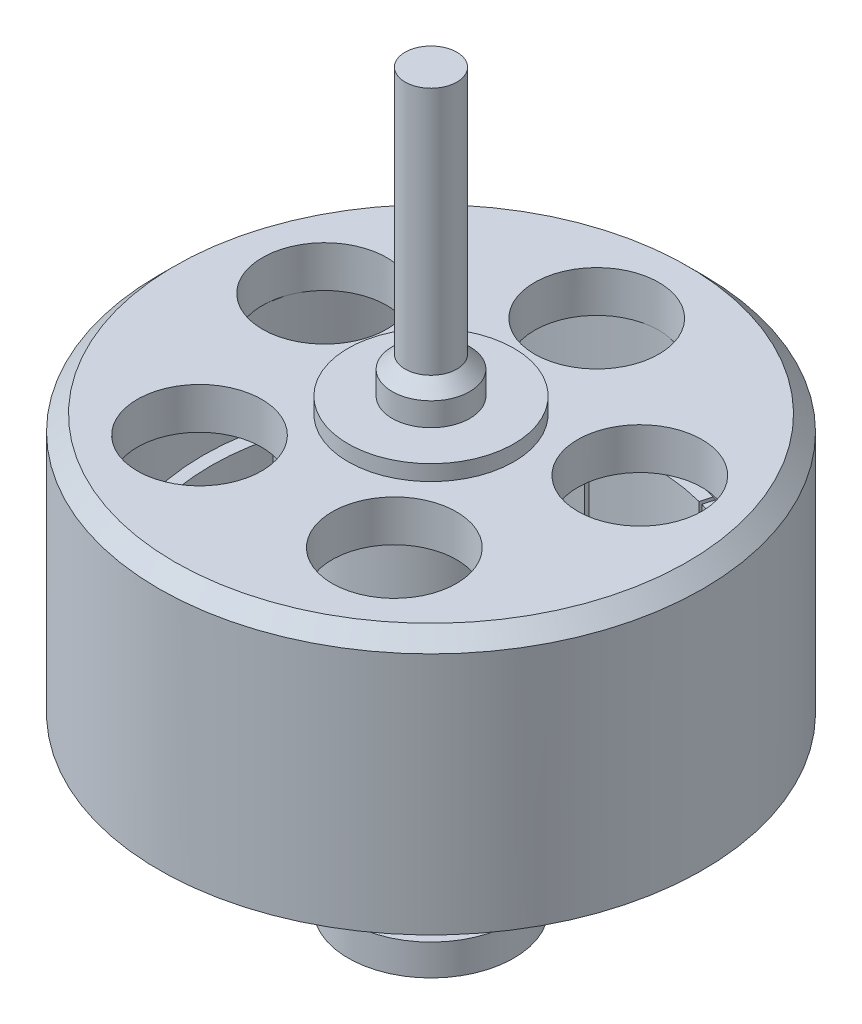
SolidWorks part; units mm, degrees
ref_plane "Front Plane" through (0, 0, 0) normal (0, 0, 1) x (1, 0, 0)
ref_plane "Top Plane" through (0, 0, 0) normal (0, 1, 0) x (1, 0, 0)
ref_plane "Right Plane" through (0, 0, 0) normal (1, 0, 0) x (0, 0, -1)
sketch "Sketch2" plane through (0, 0, 0) normal (1, 0, 0) x (0, 0, -1)
  line L0 (0, -2.1) -> (0, 2.1) construction
  line L1 (0, 2.1) -> (4.9, 2.1)
  line L2 (4.9, 2.1) -> (4.9, -2.1)
  line L3 (4.9, -2.1) -> (5.25, -2.1)
  line L4 (5.25, -2.1) -> (5.25, 2.9)
  line L5 (5.25, 2.9) -> (0, 2.9)
  line L6 (0, 2.9) -> (0, 2.1)
  point P4 (0, 0)
  dimension "D1" = 5.25
  dimension "D2" = 4.2
  dimension "D3" = 0.35
  dimension "D4" = 5
revolve "Revolve1" add sketch "Sketch2" angle 360 about L0
sketch "Sketch3" plane through (0, 2.9, 0) normal (0, 1, 0) x (1, 0, 0)
  line L1 (0, 3.2) -> (-3.0434, 0.9889) construction
  line L2 (-3.0434, 0.9889) -> (-1.8809, -2.5889) construction
  line L3 (-1.8809, -2.5889) -> (1.8809, -2.5889) construction
  line L4 (1.8809, -2.5889) -> (3.0434, 0.9889) construction
  line L5 (3.0434, 0.9889) -> (0, 3.2) construction
  circle A0 centre (0, 0) radius 2.5889 construction
  circle A1 centre (0, 3.2) radius 1.2
  circle A2 centre (3.0434, 0.9889) radius 1.2
  circle A3 centre (1.8809, -2.5889) radius 1.2
  circle A4 centre (-1.8809, -2.5889) radius 1.2
  circle A5 centre (-3.0434, 0.9889) radius 1.2
  circle A6 centre (0, 0) radius 5.25 construction
  point P13 (0, 4.4)
  point P16 (0, 5.25)
  dimension "D1" = 2.4
  dimension "D2" = 0.85
extrude "Cut-Extrude1" cut sketch "Sketch3" against normal through all
sketch "Sketch4" plane through (0, -2.1, 0) normal (0, -1, 0) x (1, 0, 0)
  line L0 (1.0641, -4.1146) -> (1.2269, -4.7439)
  line L1 (-1.0641, -4.1146) -> (-1.2269, -4.7439)
  line L2 (-1.0641, -4.1146) -> (0, 0) construction
  line L3 (0, 0) -> (1.0641, -4.1146) construction
  arc A0 (1.0641, -4.1146) -> (-1.0641, -4.1146) centre (0, 0) cw
  arc A1 (1.2269, -4.7439) -> (-1.2269, -4.7439) centre (0, 0) cw
  circle A2 centre (0, 0) radius 4.9 construction
  circle A3 centre (0, 0) radius 5.25 construction
  point P9 (0, -5.25)
  point P13 (0, -4.25)
  dimension "D1" = 29
  dimension "D2" = 1
extrude "Boss-Extrude1" add sketch "Sketch4" against normal blind 2 from offset 0.01 offset against normal yes
pattern_circular "CirPattern1" count 12 over 360 about axis through (0, 0, 0) along (0, 1, 0) of "Boss-Extrude1"
chamfer "Chamfer1" distance 0.3 angle 45 1 edges at (0, 2.9, -5.25)
sketch "Sketch6" plane through (0, 0, 0) normal (0, 0, 1) x (1, 0, 0)
  line L0 (4.95, 2.9) -> (-4.95, 2.9) construction
  line L1 (0, -6.1) -> (0.5, -6.1)
  line L2 (0, -6.1) -> (0, 8.7)
  line L3 (0, 8.7) -> (0.5, 8.7)
  line L4 (0.5, -6.1) -> (0.5, 8.7)
  line L5 (-5.25, -2.1) -> (5.25, -2.1) construction
  dimension "D1" = 5.8
  dimension "D2" = 0.5
  dimension "D3" = 4
revolve "Revolve2" add sketch "Sketch6" angle 360 about L2
sketch "Sketch7" plane through (0, 0, 0) normal (0, 0, 1) x (1, 0, 0)
  line L0 (-0.5, -6.1) -> (0.5, -6.1) construction
  line L1 (0, 2.9) -> (1.6, 2.9)
  line L2 (0, 2.9) -> (0, 3.2)
  line L4 (1.6, 2.9) -> (1.6, 3.2)
  line L5 (0, -5.4) -> (1.6, -5.4)
  line L6 (0, -5.4) -> (0, -4.8)
  line L7 (0, -4.8) -> (1.6, -4.8)
  line L8 (1.6, -5.4) -> (1.6, -4.8)
  line L9 (4.95, 2.9) -> (-4.95, 2.9) construction
  line L10 (0, 3.9) -> (0.5, 3.9)
  line L11 (0.5, 3.9) -> (0.75, 3.65)
  line L12 (0.75, 3.65) -> (0.75, 3.2)
  line L13 (0.75, 3.2) -> (0, 3.2) construction
  line L14 (0, 3.2) -> (0, 3.9)
  line L15 (0.5, 8.7) -> (-0.5, 8.7) construction
  line L16 (0.75, 3.2) -> (1.6, 3.2)
  line L17 (0.5, 2.9) -> (0.5, 8.7) construction
  dimension "D1" = 1.3
  dimension "D2" = 0.6
  dimension "D3" = 1.6
  dimension "D4" = 0.3
  dimension "D5" = 4.8
  dimension "D6" = 0.75
  dimension "D7" = 45
revolve "Revolve3" add sketch "Sketch7" angle 360 about L14
sketch "Sketch8" plane through (0, 0, 0) normal (0, 0, 1) x (1, 0, 0)
  line L0 (-0.5, 2.1) -> (0.5, 2.1) construction
  line L1 (0, 2.1) -> (1.8, 2.1)
  line L2 (0, 2.1) -> (0, 0.6)
  line L3 (0, 0.6) -> (1.8, 0.6)
  line L4 (1.8, 2.1) -> (1.8, 0.6)
  line L7 (-0.5, -6.1) -> (0.5, -6.1) construction
  dimension "D1" = 6.7
  dimension "D2" = 1.8
revolve "Revolve4" add sketch "Sketch8" angle 360 about L2
sketch "Sketch9" plane through (0, 2.1, 0) normal (0, -1, 0) x (1, 0, 0)
  circle A0 centre (0, 0) radius 4.4
  circle A2 centre (-3.0434, -0.9889) radius 1.2 construction
  circle A3 centre (0, 0) radius 4.9
  circle A4 centre (0, 0) radius 4.9
  circle A5 centre (0, -3.2) radius 1.2 construction
  circle A6 centre (3.0434, -0.9889) radius 1.2 construction
  circle A7 centre (1.8809, 2.5889) radius 1.2 construction
  circle A8 centre (-1.8809, 2.5889) radius 1.2 construction
  circle A9 centre (-3.0434, -0.9889) radius 1.2
  circle A10 centre (0, -3.2) radius 1.2
  circle A11 centre (3.0434, -0.9889) radius 1.2
  circle A12 centre (1.8809, 2.5889) radius 1.2
  circle A13 centre (-1.8809, 2.5889) radius 1.2
  circle M6 centre (-3.0434, -0.9889) radius 1.2
  circle M7 centre (-1.8809, 2.5889) radius 1.2
  circle M8 centre (1.8809, 2.5889) radius 1.2
  circle M9 centre (3.0434, -0.9889) radius 1.2
  circle M10 centre (0, -3.2) radius 1.2
  circle M11 centre (0, 0) radius 4.9
  dimension "D1" = 0
extrude "Boss-Extrude2" add sketch "Sketch9" along normal offset from surface (2.09 mm away) 0.1 contours A0 M11 M10 M6 M7 M8 M9
